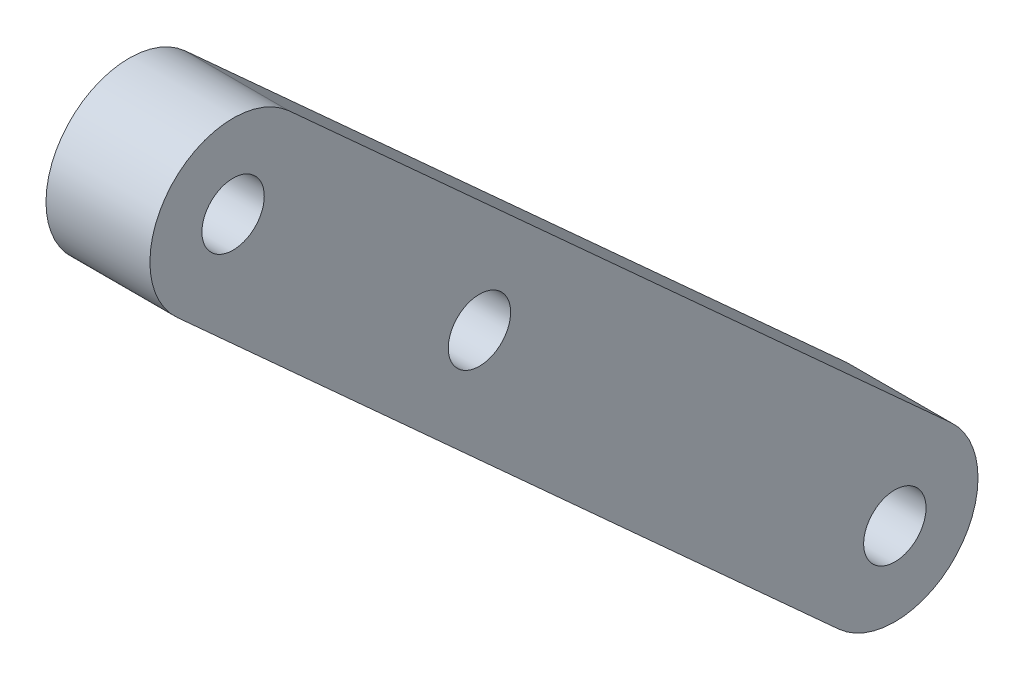
SolidWorks part; units mm, degrees
ref_plane "Front Plane" through (0, 0, 0) normal (0, 0, 1) x (1, 0, 0)
ref_plane "Top Plane" through (0, 0, 0) normal (0, 1, 0) x (1, 0, 0)
ref_plane "Right Plane" through (0, 0, 0) normal (1, 0, 0) x (0, 0, -1)
sketch "Sketch2" plane through (0, 0, 0) normal (1, 0, 0) x (0, 0, -1)
  line L0 (37.5141, -280.4428) -> (195.2536, -280.4428) construction
  line L1 (0, 0) -> (130, 0)
  line L2 (60.5168, 62.6667) -> (92.3525, 33.7619)
  line L3 (55.1391, 56.7438) -> (86.9748, 27.839)
  line L4 (57.8279, 59.7053) -> (89.6636, 30.8005) construction
  circle A0 centre (89.6636, 30.8005) radius 4
  circle A1 centre (57.8279, 59.7053) radius 4
  circle A2 centre (89.6636, 30.8005) radius 1.5
  circle A3 centre (57.8279, 59.7053) radius 1.5
  circle A4 centre (69.6793, 48.945) radius 1.5
  dimension "D2" = 8
  dimension "D3" = 8
  dimension "D5" = 3
  dimension "D6" = 3
  dimension "D7" = 3
  dimension "D1" = 130
  dimension "D4" = 43
  dimension "D8" = 16.0075
extrude "Boss-Extrude1" add sketch "Sketch2" along normal blind 5 contours A1 L3 A0 L2 A4 | A1 A3 | A0 A2
